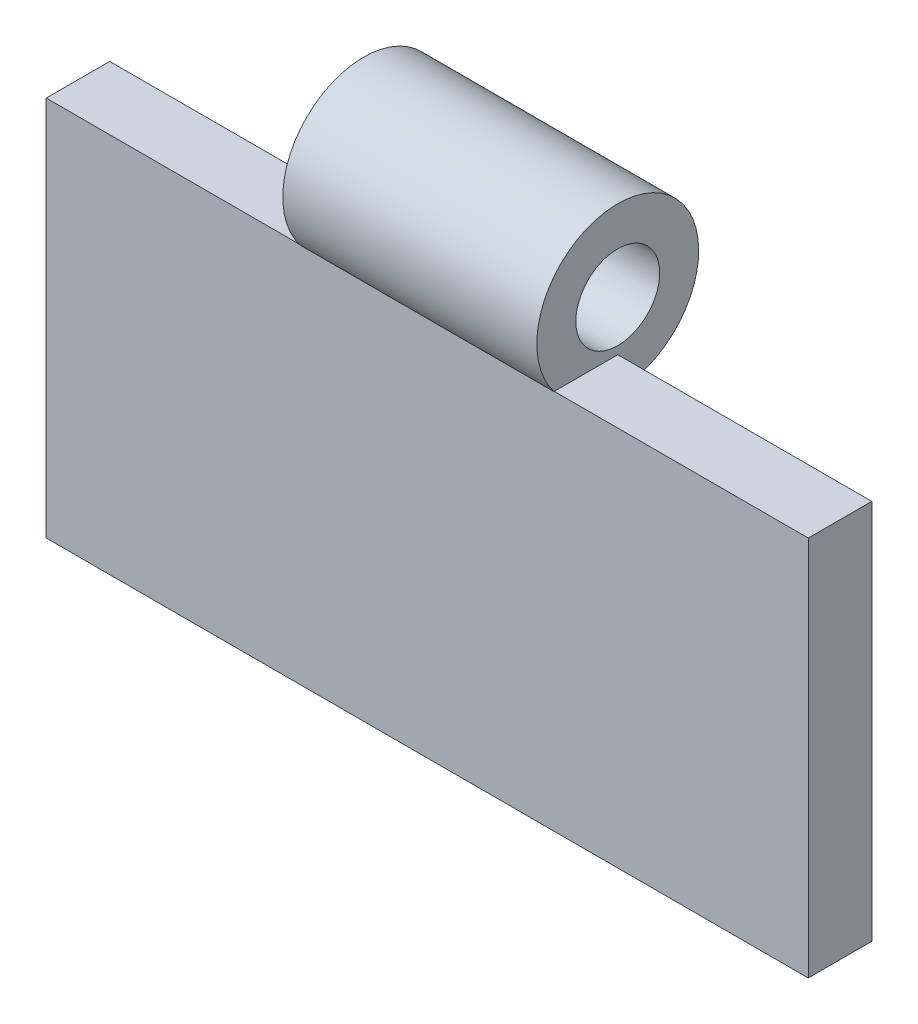
SolidWorks part; units mm, degrees
ref_plane "Front Plane" through (0, 0, 0) normal (0, 0, 1) x (1, 0, 0)
ref_plane "Top Plane" through (0, 0, 0) normal (0, 1, 0) x (1, 0, 0)
ref_plane "Right Plane" through (0, 0, 0) normal (1, 0, 0) x (0, 0, -1)
sketch "Sketch1" plane through (0, 0, 0) normal (0, 0, 1) x (1, 0, 0)
  line L1 (0, 0) -> (60, 0)
  line L2 (0, 0) -> (0, -30)
  line L3 (0, -30) -> (60, -30)
  line L4 (60, 0) -> (60, -30)
extrude "Boss-Extrude1" add sketch "Sketch1" along normal blind 5
sketch "Sketch6" plane through (20, 0, 0) normal (-1, 0, 0) x (0, 0, 1)
  circle A0 centre (0, 3.9244) radius 6.3749
  circle A1 centre (0, 3.9244) radius 3.3029
extrude "Boss-Extrude5" add sketch "Sketch6" against normal blind 20 contours A0 | A1
